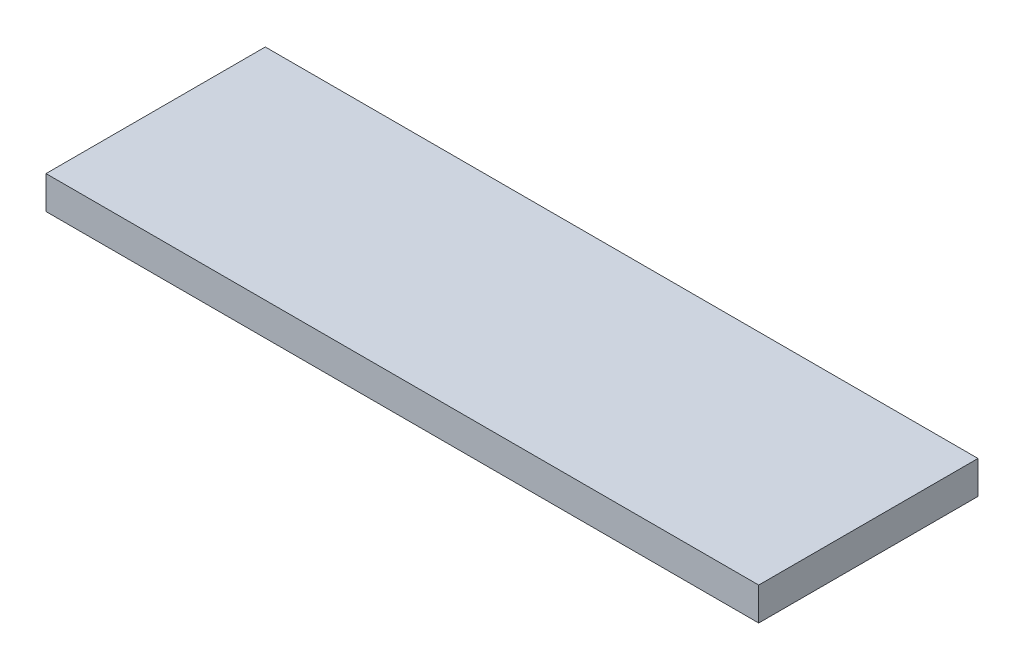
SolidWorks part; units mm, degrees
material "Acryl (halb- bis hochschlagzäh)"
ref_plane "Ebene vorne" through (0, 0, 0) normal (0, 0, 1) x (1, 0, 0)
ref_plane "Ebene oben" through (0, 0, 0) normal (0, 1, 0) x (1, 0, 0)
ref_plane "Ebene rechts" through (0, 0, 0) normal (1, 0, 0) x (0, 0, -1)
sketch "Skizze1" plane through (0, 0, 0) normal (0, 1, 0) x (1, 0, 0)
  line L1 (-32.5, -10) -> (32.5, -10)
  line L2 (-32.5, -10) -> (-32.5, 10)
  line L3 (-32.5, 10) -> (32.5, 10)
  line L4 (32.5, -10) -> (32.5, 10)
  line L5 (-32.5, -10) -> (32.5, 10) construction
  line L6 (-32.5, 10) -> (32.5, -10) construction
  point P0 (0, 0)
  dimension "D1" = 20
  dimension "D2" = 65
extrude "Aufsatz-Linear austragen1" add sketch "Skizze1" along normal blind 3
